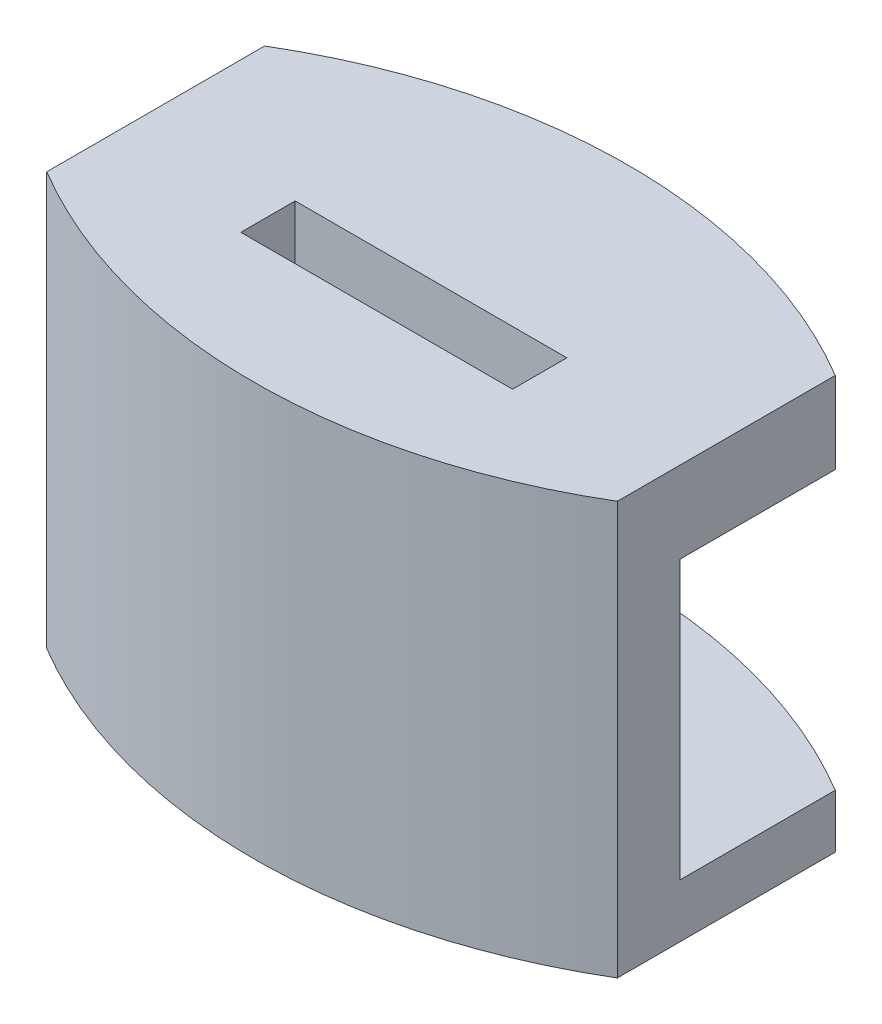
SolidWorks part; units mm, degrees
ref_plane "Front Plane" through (0, 0, 0) normal (0, 0, 1) x (1, 0, 0)
ref_plane "Top Plane" through (0, 0, 0) normal (0, 1, 0) x (1, 0, 0)
ref_plane "Right Plane" through (0, 0, 0) normal (1, 0, 0) x (0, 0, -1)
sketch "Sketch1" plane through (0, 0, 0) normal (0, 1, 0) x (1, 0, 0)
  line L1 (18.4048, -7.3) -> (-18.4048, -7.3)
  line L2 (18.4048, -7.3) -> (18.4048, 7.3)
  line L4 (-18.4048, -7.3) -> (-18.4048, 7.3)
  line L7 (-18.4048, 7.3) -> (-18.4048, 11.4716)
  line L9 (18.4048, 11.4716) -> (18.4048, 7.3)
  arc A0 (-18.4048, 11.4716) -> (18.4048, 11.4716) centre (0, 20.5) ccw
  dimension "D1" = 36.8097
extrude "Boss-Extrude1" add sketch "Sketch1" along normal blind 15.22
sketch "Sketch2" plane through (0, 15.22, 0) normal (0, 1, 0) x (1, 0, 0)
  line L1 (-18.4048, -7.3) -> (18.4048, -7.3)
  line L2 (-18.4048, -7.3) -> (-18.4048, 18.7716)
  line L3 (-18.4048, 18.7716) -> (18.4048, 18.7716)
  line L4 (18.4048, -7.3) -> (18.4048, 18.7716)
  dimension "D1" = 7.3
extrude "Boss-Extrude2" add sketch "Sketch2" against normal blind 3
sketch "Sketch3" plane through (0, 0, 0) normal (0, -1, 0) x (1, 0, 0)
  line L1 (18.4048, 7.3) -> (-18.4048, 7.3)
  line L2 (18.4048, 7.3) -> (18.4048, -18.7716)
  line L3 (18.4048, -18.7716) -> (-18.4048, -18.7716)
  line L4 (-18.4048, 7.3) -> (-18.4048, -18.7716)
extrude "Boss-Extrude3" add sketch "Sketch3" against normal blind 2
sketch "Sketch4" plane through (0, 0, 0) normal (0, -1, 0) x (1, 0, 0)
  line L1 (-10.5, 52.2585) -> (10.5, 52.2585)
  line L2 (-10.5, 52.2585) -> (-10.5, -59.5089)
  line L3 (-10.5, -59.5089) -> (10.5, -59.5089)
  line L4 (10.5, 52.2585) -> (10.5, -59.5089)
  line L5 (-10.5, 52.2585) -> (10.5, -59.5089) construction
  line L6 (-10.5, -59.5089) -> (10.5, 52.2585) construction
  line L7 (-30.1806, 75.162) -> (30.1806, 75.162)
  line L8 (-30.1806, 75.162) -> (-30.1806, -82.4124)
  line L9 (-30.1806, -82.4124) -> (30.1806, -82.4124)
  line L10 (30.1806, 75.162) -> (30.1806, -82.4124)
  line L11 (-30.1806, 75.162) -> (30.1806, -82.4124) construction
  line L12 (-30.1806, -82.4124) -> (30.1806, 75.162) construction
  point P0 (0, -3.6252)
  point P5 (0, -3.6252)
  dimension "D1" = 21
  dimension "D2" = 0
extrude "Cut-Extrude1" cut sketch "Sketch4" against normal blind 38.576
sketch "Sketch5" plane through (0, 12.22, 0) normal (0, -1, 0) x (1, 0, 0)
  line L1 (-5, -2.2352) -> (5, -2.2352)
  line L2 (-5, -2.2352) -> (-5, -4.2352)
  line L3 (-5, -4.2352) -> (5, -4.2352)
  line L4 (5, -2.2352) -> (5, -4.2352)
  line L5 (-5, -2.2352) -> (5, -4.2352) construction
  line L6 (-5, -4.2352) -> (5, -2.2352) construction
  point P0 (0, -3.2352)
  point P5 (0, -2.2352)
  dimension "D1" = 10
  dimension "D2" = 2
  dimension "D3" = 0
  dimension "D4" = 2.2352
extrude "Cut-Extrude2" cut sketch "Sketch5" against normal blind 38.576
sketch "Sketch6" plane through (0, 12.22, 0) normal (0, -1, 0) x (1, 0, 0)
  line L0 (10.5, -18.7716) -> (-10.5, -18.7716) construction
  line L1 (-17.7857, -28.9316) -> (17.7857, -28.9316)
  line L2 (-17.7857, -28.9316) -> (-17.7857, -8.6116)
  line L3 (-17.7857, -8.6116) -> (17.7857, -8.6116)
  line L4 (17.7857, -28.9316) -> (17.7857, -8.6116)
  line L5 (-17.7857, -28.9316) -> (17.7857, -8.6116) construction
  line L6 (-17.7857, -8.6116) -> (17.7857, -28.9316) construction
  point P0 (0, -18.7716)
  dimension "D1" = 20.32
extrude "Cut-Extrude3" cut sketch "Sketch6" along normal blind 25.876 and the other way blind 20.32
sketch "Sketch7" plane through (0, 15.22, 0) normal (0, 1, 0) x (1, 0, 0)
  line L0 (-10.5, -7.3) -> (10.5, -7.3) construction
  line L1 (-12.7941, -9.8) -> (12.7941, -9.8)
  line L2 (-12.7941, -9.8) -> (-12.7941, -4.8)
  line L3 (-12.7941, -4.8) -> (12.7941, -4.8)
  line L4 (12.7941, -9.8) -> (12.7941, -4.8)
  line L5 (-12.7941, -9.8) -> (12.7941, -4.8) construction
  line L6 (-12.7941, -4.8) -> (12.7941, -9.8) construction
  point P0 (0, -7.3)
  dimension "D1" = 5
extrude "Cut-Extrude4" cut sketch "Sketch7" against normal blind 25.876
sketch "Sketch10" plane through (0, 15.22, 0) normal (0, 1, 0) x (1, 0, 0)
  line L1 (10.5, -4.8) -> (-10.5, -4.8) construction
  circle A0 centre (0, 18.2) radius 20.5
  circle A1 centre (0, 18.2) radius 48.6775
  point P5 (0, -4.8)
  dimension "D1" = 41
  dimension "D2" = 23
extrude "Cut-Extrude5" cut sketch "Sketch10" against normal blind 169.64 and the other way blind 14.478
sketch "Sketch11" plane through (0, 15.22, 0) normal (0, 1, 0) x (1, 0, 0)
  line L0 (-10.5, 8.6116) -> (10.5, 8.6116)
  arc A0 (-10.5, 8.6116) -> (10.5, 8.6116) centre (0, -8.9952) cw
extrude "Boss-Extrude4" add sketch "Sketch11" against normal blind 15.208
sketch "Sketch12" plane through (0, 0, 0) normal (0, -1, 0) x (1, 0, 0)
  line L1 (16.6123, 6.8658) -> (-13.8891, 6.8658)
  line L2 (16.6123, 6.8658) -> (16.6123, -18.8097)
  line L3 (16.6123, -18.8097) -> (-13.8891, -18.8097)
  line L4 (-13.8891, 6.8658) -> (-13.8891, -18.8097)
  line L5 (16.6123, 6.8658) -> (-13.8891, -18.8097) construction
  line L6 (16.6123, -18.8097) -> (-13.8891, 6.8658) construction
  point P0 (1.3616, -5.9719)
extrude "Cut-Extrude8" cut sketch "Sketch12" along normal blind 8.604 and the other way blind 0.0254
sketch "Sketch13" plane through (0, 0, -8.6116) normal (0, 0, 1) x (1, 0, 0)
  line L1 (10.5, 2) -> (-10.5, 2)
  line L2 (10.5, 2) -> (10.5, 12.22)
  line L3 (10.5, 12.22) -> (-10.5, 12.22)
  line L4 (-10.5, 2) -> (-10.5, 12.22)
extrude "Cut-Extrude9" cut sketch "Sketch13" against normal blind 8.604
